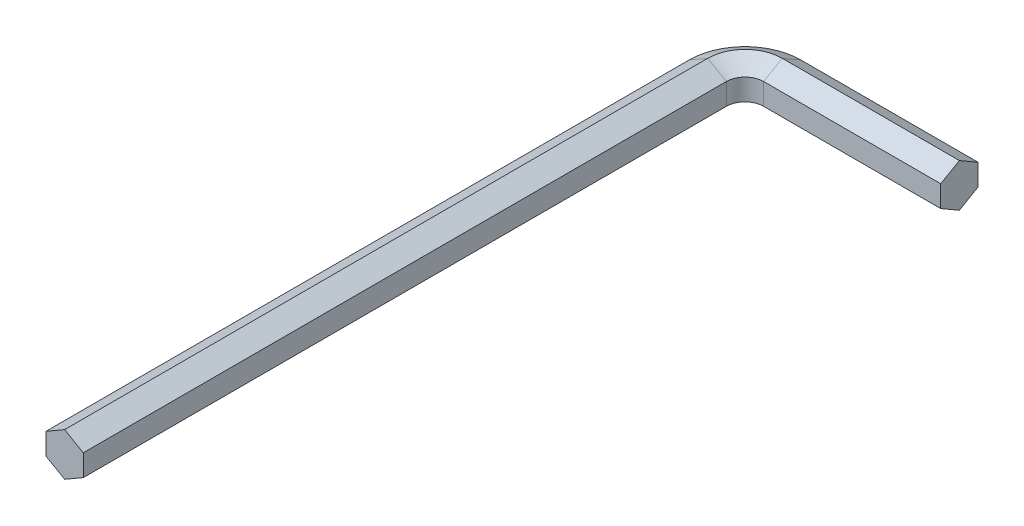
SolidWorks part; units mm, degrees
ref_plane "Front Plane" through (0, 0, 0) normal (0, 0, 1) x (1, 0, 0)
ref_plane "Top Plane" through (0, 0, 0) normal (0, 1, 0) x (1, 0, 0)
ref_plane "Right Plane" through (0, 0, 0) normal (1, 0, 0) x (0, 0, -1)
sketch "Sketch1" plane through (0, 0, 0) normal (0, 1, 0) x (1, 0, 0)
  line L0 (0, 0) -> (0, 69)
  line L1 (6, 75) -> (25, 75)
  arc A0 (0, 69) -> (6, 75) centre (6, 69) cw
  dimension "D1" = 75
  dimension "D3" = 6
  dimension "D2" = 25
ref_plane "Plane1" through (25, 0, 0) normal (1, 0, 0) x (0, 0, -1)
sketch "Sketch3" plane through (25, 0, 0) normal (1, 0, 0) x (0, 0, -1)
  line L0 (75, 0) -> (69, 0) construction
  line L1 (75, -1.1547) -> (75, 1.1547)
  line L2 (75, 1.1547) -> (73, 2.3094)
  line L3 (73, 2.3094) -> (71, 1.1547)
  line L4 (71, 1.1547) -> (71, -1.1547)
  line L5 (71, -1.1547) -> (73, -2.3094)
  line L6 (73, -2.3094) -> (75, -1.1547)
  circle A0 centre (73, 0) radius 2 construction
  dimension "D1" = 4
  dimension "D2" = 75
sweep "Sweep2" add profiles "Sketch3" path "Sketch1"
